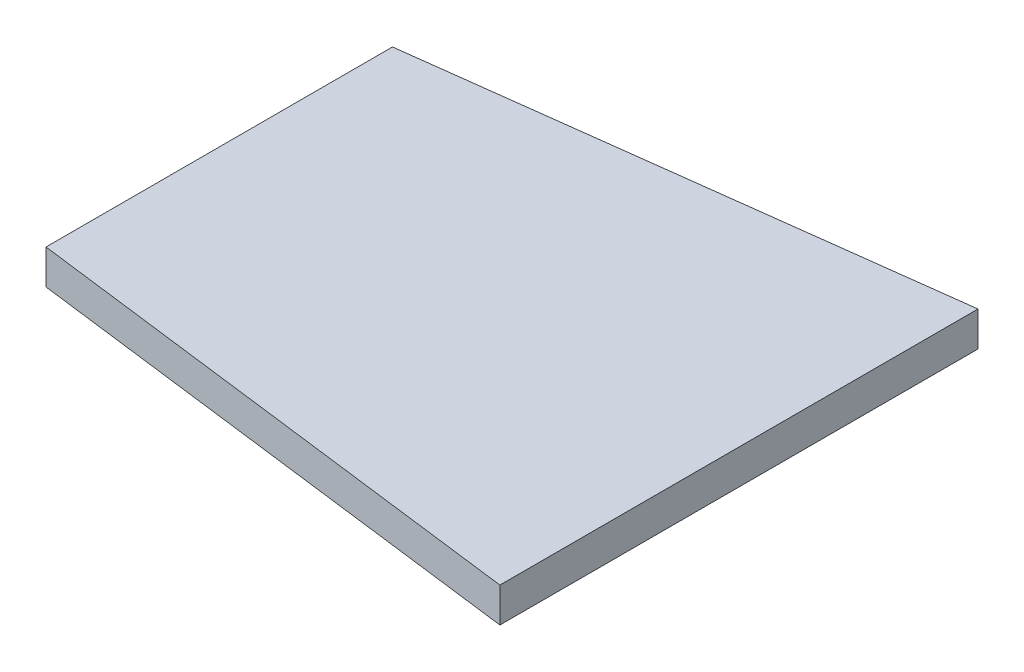
SolidWorks part; units mm, degrees
ref_plane "Front Plane" through (0, 0, 0) normal (0, 0, 1) x (1, 0, 0)
ref_plane "Top Plane" through (0, 0, 0) normal (0, 1, 0) x (1, 0, 0)
ref_plane "Right Plane" through (0, 0, 0) normal (1, 0, 0) x (0, 0, -1)
sketch "Sketch1" plane through (0, 0, 0) normal (0, 1, 0) x (1, 0, 0)
  line L0 (0, 25) -> (75, 34.5)
  line L1 (0, -25) -> (75, -25) construction
  line L2 (0, -25) -> (0, 25)
  line L3 (0, 25) -> (75, 25) construction
  line L4 (75, -25) -> (75, 25) construction
  line L5 (75, 34.5) -> (75, -34.5)
  line L6 (0, -25) -> (75, -34.5)
  point P5 (0, 0)
  point P8 (75, 0)
  point P9 (75, 0)
  point P10 (75, -50.9743)
  dimension "D1" = 75
  dimension "D2" = 50
  dimension "D3" = 69
extrude "Boss-Extrude1" add sketch "Sketch1" along normal blind 5
sketch "Sketch2" plane through (0, 5, 0) normal (0, 1, 0) x (1, 0, 0)
  line L0 (37.5, 29.75) -> (37.5, -29.75)
  line L1 (75, 34.5) -> (0, 25) construction
  line L2 (0, -25) -> (75, -34.5) construction
